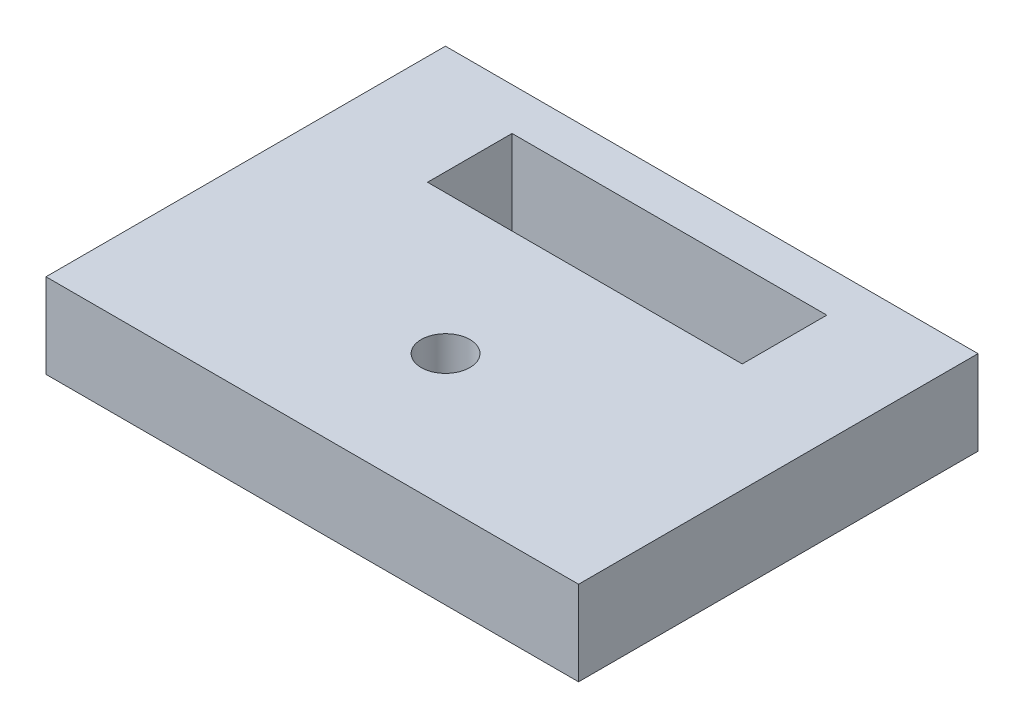
SolidWorks part; units mm, degrees
ref_plane "Front Plane" through (0, 0, 0) normal (0, 0, 1) x (1, 0, 0)
ref_plane "Top Plane" through (0, 0, 0) normal (0, 1, 0) x (1, 0, 0)
ref_plane "Right Plane" through (0, 0, 0) normal (1, 0, 0) x (0, 0, -1)
sketch "Sketch1" plane through (0, 0, 0) normal (0, 1, 0) x (1, 0, 0)
  line L0 (-20, -15) -> (-20, 15)
  line L1 (-20, -15) -> (20, -15)
  line L2 (-20, 15) -> (20, 15)
  line L3 (20, -15) -> (20, 15)
  line L4 (-20, -15) -> (20, 15) construction
  line L5 (-20, 15) -> (20, -15) construction
  point P1 (0, 0)
  dimension "D1" = 30
  dimension "D2" = 40
extrude "Boss-Extrude1" add sketch "Sketch1" along normal blind 6.35
sketch "Sketch2" plane through (0, 6.35, 0) normal (0, 1, 0) x (1, 0, 0)
  line L0 (-11.82, 5.475) -> (-11.82, 11.825)
  line L1 (-11.82, 5.475) -> (11.82, 5.475)
  line L2 (-11.82, 11.825) -> (11.82, 11.825)
  line L3 (11.82, 5.475) -> (11.82, 11.825)
  line L4 (-11.82, 5.475) -> (11.82, 11.825) construction
  line L5 (-11.82, 11.825) -> (11.82, 5.475) construction
  line L6 (20, 15) -> (-20, 15) construction
  point P1 (0, 8.65)
  dimension "D1" = 6.35
  dimension "D2" = 23.64
  dimension "D3" = 6.35
extrude "Cut-Extrude1" cut sketch "Sketch2" against normal through all
sketch "Sketch3" plane through (0, 6.35, 0) normal (0, 1, 0) x (1, 0, 0)
  line L0 (-11.82, 5.475) -> (11.82, 5.475) construction
  point P0 (0, -4.9898)
  dimension "D1" = 10.4648
hole_wizard "#6 Clearance Hole1" positions "Sketch5" profile "Sketch4" hole size "#6" standard "ANSI Inch" end condition through all
sketch "Sketch5" plane through (0, 6.35, 0) normal (0, 1, 0) x (1, 0, 0)
  point P0 (0, -4.9898)
sketch "Sketch4" plane through (0, 6.35, 4.9898) normal (1, 0, 0) x (0, 0, 1)
  line L0 (0, 0) -> (0, 6.35)
  line L1 (0, 6.35) -> (1.8288, 6.35)
  line L2 (1.8288, 6.35) -> (1.8288, 0)
  line L5 (1.8288, 0) -> (0, 0)
  line L11 (0, -6.35) -> (0, 107.95) construction
  dimension "Thru Hole Dia." = 3.6576
  dimension "Thru Hole Depth" = 6.35
